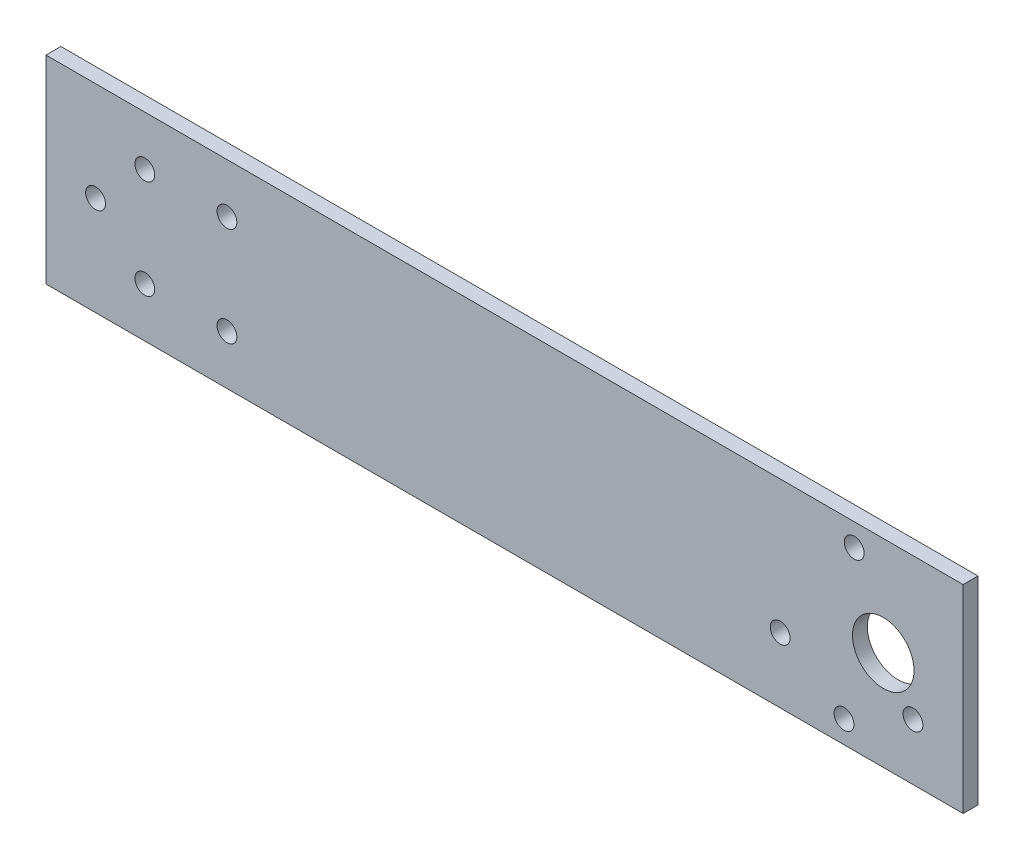
SolidWorks part; units mm, degrees
ref_plane "Front Plane" through (0, 0, 0) normal (0, 0, 1) x (1, 0, 0)
ref_plane "Top Plane" through (0, 0, 0) normal (0, 1, 0) x (1, 0, 0)
ref_plane "Right Plane" through (0, 0, 0) normal (1, 0, 0) x (0, 0, -1)
sketch "Sketch1" plane through (0, 0, 0) normal (0, 0, 1) x (1, 0, 0)
  line L0 (0, 0) -> (0, 40)
  line L1 (0, 40) -> (185, 40)
  line L2 (0, 0) -> (185, 0)
  line L3 (185, 40) -> (185, 0)
  line L4 (-1.3729, 20) -> (30.8932, 20) construction
  line L5 (19.9303, 20) -> (19.9303, 30) construction
  line L6 (19.9303, 20) -> (19.9303, 10) construction
  line L7 (29.5, 40) -> (29.5, 0) construction
  line L8 (27, 0) -> (27, 40) construction
  line L10 (143, 40) -> (143, 0) construction
  line L11 (140.5, 0) -> (140.5, 40) construction
  line L12 (70.5, 40) -> (70.5, 0) construction
  line L13 (69.5, 40) -> (69.5, 0) construction
  circle A0 centre (10, 20) radius 2
  circle A1 centre (162, 20) radius 18.5 construction
  circle A2 centre (19.9303, 10) radius 2
  circle A3 centre (19.9303, 30) radius 2
  circle A4 centre (160.9709, 4.5342) radius 2
  circle A5 centre (148.0917, 13.1583) radius 2
  circle A6 centre (174.8792, 11.3759) radius 2
  circle A7 centre (163.0291, 35.4658) radius 2
  circle A8 centre (168.8417, 6.0917) radius 2 construction
  circle A9 centre (170.6241, 32.8792) radius 2 construction
  circle A10 centre (146.5342, 21.0291) radius 2 construction
  circle A11 centre (168.8841, 20) radius 6.207
  circle A12 centre (168.8841, 20) radius 3.0239
  circle A13 centre (36.5, 30) radius 2
  circle A14 centre (36.5, 10) radius 2
  point P30 (162, 20)
  point P52 (36.9895, 20)
  dimension "D5" = 4
  dimension "D6" = 10
  dimension "D7" = 4
  dimension "D8" = 40
  dimension "D9" = 4
  dimension "D11" = 4
  dimension "D17" = 4
  dimension "D1" = 40
  dimension "D2" = 185
  dimension "D3" = 10
  dimension "D4" = 10
  dimension "D10" = 2.5
  dimension "D12" = 23
  dimension "D13" = 42
  dimension "D14" = 2.5
  dimension "D15" = 70
  dimension "D16" = 1
  dimension "D18" = 7
  dimension "D19" = 7
  dimension "D20" = 10
  dimension "D21" = 10
extrude "Boss-Extrude1" add sketch "Sketch1" along normal blind 3 contours L3 L1 L0 L2 A14 A13 A11 A7 A6 A5 A4 A3 A2 A0
